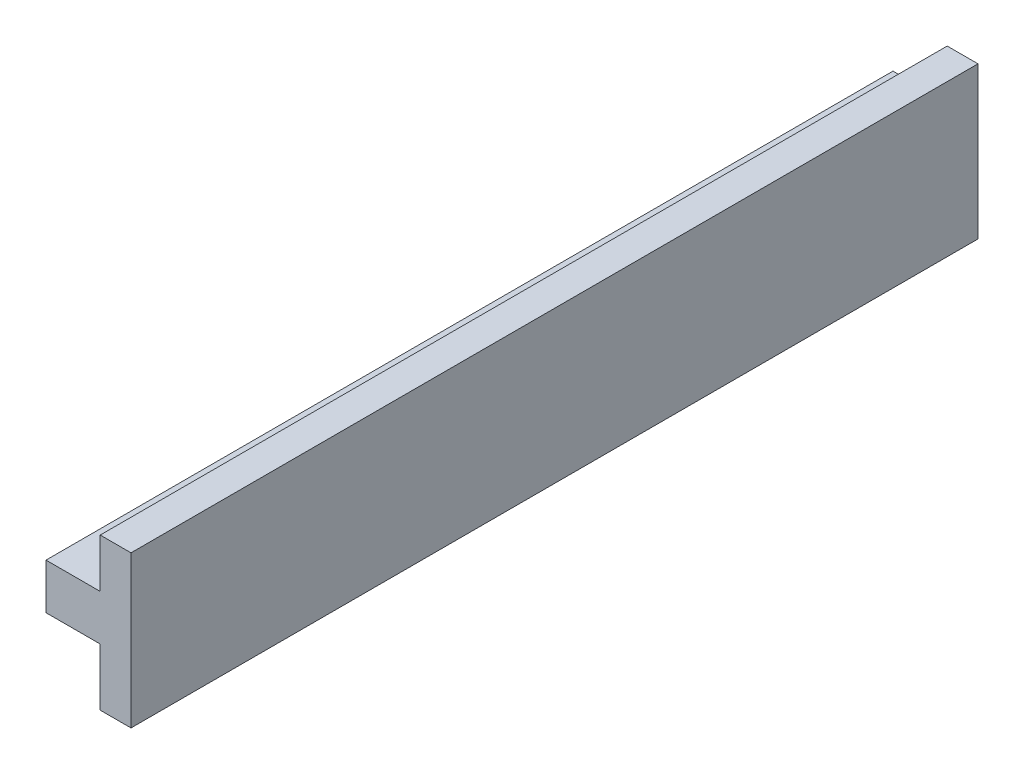
SolidWorks part; units mm, degrees
ref_plane "Front Plane" through (0, 0, 0) normal (0, 0, 1) x (1, 0, 0)
ref_plane "Top Plane" through (0, 0, 0) normal (0, 1, 0) x (1, 0, 0)
ref_plane "Right Plane" through (0, 0, 0) normal (1, 0, 0) x (0, 0, -1)
sketch "Sketch1" plane through (0, 0, -35.1738) normal (0, 0, 1) x (1, 0, 0)
  line L0 (79.4986, 40.052) -> (106.5851, 40.052) construction
  line L1 (85.9614, 43.752) -> (94.7614, 43.752)
  line L2 (94.7614, 36.352) -> (85.9614, 36.352)
  line L3 (85.9614, 36.352) -> (85.9614, 43.752)
  line L4 (94.7614, 51.6762) -> (94.7614, 27.052) construction
  line L5 (99.7614, 51.6762) -> (99.7614, 27.052)
  line L6 (99.7614, 51.6762) -> (94.7614, 51.6762)
  line L7 (94.7614, 51.6762) -> (94.7614, 43.752)
  line L8 (99.7614, 27.052) -> (94.7614, 27.052)
  line L9 (94.7614, 27.052) -> (94.7614, 36.352)
  dimension "D1" = 5
ref_plane "Plane3" through (0, 0, -41.2738) normal (0, 0, 1) x (1, 0, 0)
sketch "Sketch4" plane through (0, 0, -41.2738) normal (0, 0, 1) x (1, 0, 0)
  line L0 (99.7614, 51.6762) -> (99.7614, 27.052) construction
  line L1 (99.7614, 51.6762) -> (94.7614, 51.6762) construction
  line L2 (94.7614, 51.6762) -> (94.7614, 43.752) construction
  line L3 (85.9614, 43.752) -> (94.7614, 43.752) construction
  line L4 (85.9614, 36.352) -> (85.9614, 43.752) construction
  line L5 (94.7614, 36.352) -> (85.9614, 36.352) construction
  line L6 (94.7614, 27.052) -> (94.7614, 36.352) construction
  line L7 (99.7614, 27.052) -> (94.7614, 27.052) construction
  line L8 (99.7614, 51.6762) -> (99.7614, 27.052)
  line L9 (99.7614, 51.6762) -> (94.7614, 51.6762)
  line L10 (94.7614, 51.6762) -> (94.7614, 43.752)
  line L11 (85.9614, 43.752) -> (94.7614, 43.752)
  line L12 (85.9614, 36.352) -> (85.9614, 43.752)
  line L13 (94.7614, 36.352) -> (85.9614, 36.352)
  line L14 (94.7614, 27.052) -> (94.7614, 36.352)
  line L15 (99.7614, 27.052) -> (94.7614, 27.052)
extrude "Extrude2" add sketch "Sketch1" against normal blind 137.5
